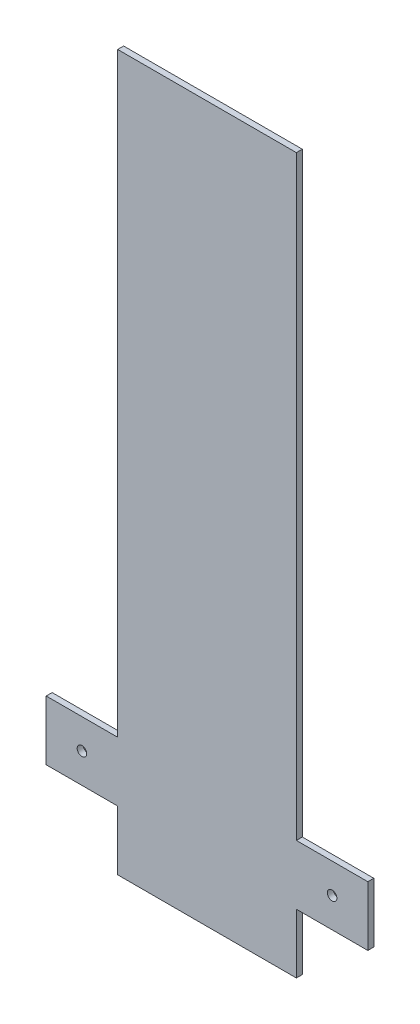
SolidWorks part; units mm, degrees
ref_plane "Front Plane" through (0, 0, 0) normal (0, 0, 1) x (1, 0, 0)
ref_plane "Top Plane" through (0, 0, 0) normal (0, 1, 0) x (1, 0, 0)
ref_plane "Right Plane" through (0, 0, 0) normal (1, 0, 0) x (0, 0, -1)
sketch "Sketch2" plane through (0, 0, 0) normal (0, 0, 1) x (1, 0, 0)
  line L0 (75, 300) -> (75, -200)
  line L1 (75, -200) -> (135, -200)
  line L2 (-75, 300) -> (-75, -200)
  line L3 (-75, -200) -> (-135, -200)
  line L4 (-135, -200) -> (-135, -250)
  line L5 (-135, -250) -> (-75, -250)
  line L6 (-75, -250) -> (-75, -300)
  line L7 (-75, -300) -> (75, -300)
  line L9 (75, 300) -> (-75, 300)
  line L10 (135, -200) -> (135, -250)
  line L11 (135, -250) -> (75, -250)
  line L12 (75, -250) -> (75, -300)
  circle A0 centre (-105, -225) radius 4
  circle A1 centre (105, -225) radius 4
  dimension "D1" = 500
  dimension "D7" = 8
  dimension "D2" = 50
  dimension "D3" = 30
  dimension "D4" = 60
  dimension "D5" = 50
  dimension "D6" = 150
extrude "Boss-Extrude1" add sketch "Sketch2" along normal blind 5
